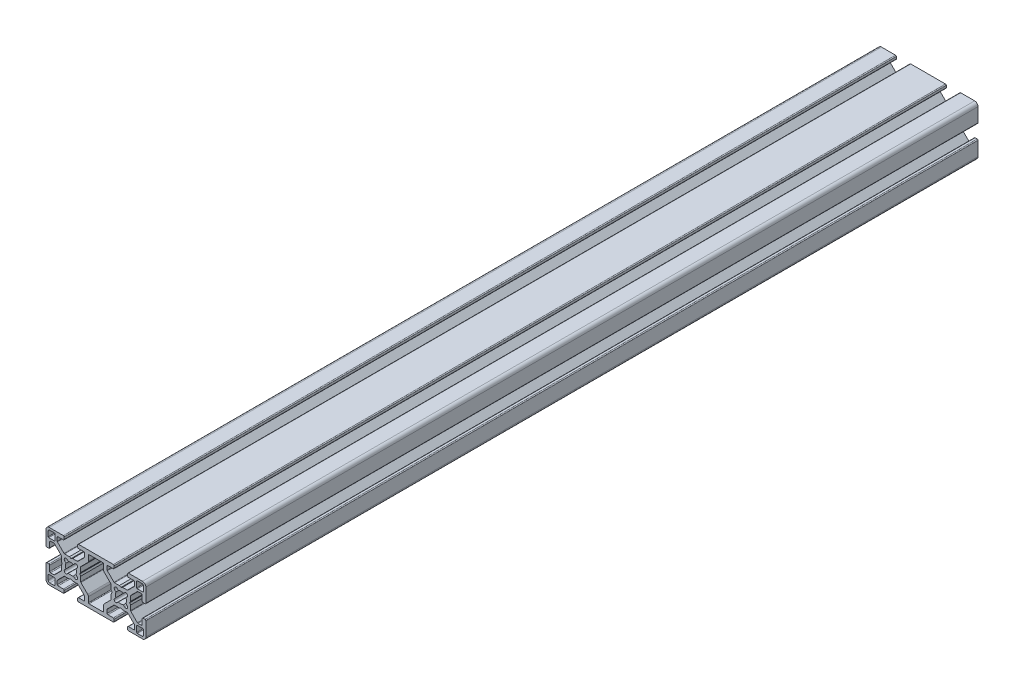
SolidWorks part; units mm, degrees
material "6105-T5 Aluminum"
ref_plane "Front Plane" through (0, 0, 0) normal (0, 0, 1) x (1, 0, 0)
ref_plane "Top Plane" through (0, 0, 0) normal (0, 1, 0) x (1, 0, 0)
ref_plane "Right Plane" through (0, 0, 0) normal (1, 0, 0) x (0, 0, -1)
sketch "Sketch1" plane through (0, 0, 0) normal (0, 0, 1) x (1, 0, 0)
  line L0 (12.7825, 3.7261) -> (13.5257, 2.983)
  line L1 (16.4743, 2.983) -> (17.2175, 3.7261)
  line L2 (18.7261, 2.2175) -> (17.983, 1.4743)
  line L3 (17.983, -1.4743) -> (18.7261, -2.2175)
  line L4 (17.2175, -3.7261) -> (16.4743, -2.983)
  line L5 (13.5257, -2.983) -> (12.7825, -3.7261)
  line L6 (11.2739, -2.2175) -> (12.017, -1.4743)
  line L7 (12.017, 1.4743) -> (11.2739, 2.2175)
  line L8 (-28.7046, 9.8946) -> (-28.7046, 12.6886)
  line L9 (-27.6886, 13.7046) -> (-24.8946, 13.7046)
  line L10 (-24.5136, 13.3236) -> (-24.5136, 9.8946)
  line L11 (-24.8946, 9.5136) -> (-28.3236, 9.5136)
  line L12 (-24.8946, -13.7046) -> (-27.6886, -13.7046)
  line L13 (-28.7046, -12.6886) -> (-28.7046, -9.8946)
  line L14 (-28.3236, -9.5136) -> (-24.8946, -9.5136)
  line L15 (-24.5136, -9.8946) -> (-24.5136, -13.3236)
  line L16 (4.9816, 8.2224) -> (9.0292, 4.1748)
  line L17 (9.178, 3.8155) -> (9.178, 0.9525)
  line L18 (9.178, 0.9525) -> (9.686, 0)
  line L19 (9.686, 0) -> (9.178, -0.9525)
  line L20 (9.178, -0.9525) -> (9.178, -3.8155)
  line L21 (9.0292, -4.1748) -> (4.9816, -8.2224)
  line L22 (4.5352, -9.3) -> (4.5352, -12.4092)
  line L23 (4.1542, -12.7902) -> (-4.1542, -12.7902)
  line L24 (-4.5352, -12.4092) -> (-4.5352, -9.3)
  line L25 (-4.9816, -8.2224) -> (-9.0292, -4.1748)
  line L26 (-9.178, -3.8155) -> (-9.178, -0.9525)
  line L27 (-9.178, -0.9525) -> (-9.686, 0)
  line L28 (-9.686, 0) -> (-9.178, 0.9525)
  line L29 (-9.178, 0.9525) -> (-9.178, 3.8155)
  line L30 (-9.0292, 4.1748) -> (-4.9816, 8.2224)
  line L31 (-4.5352, 9.3) -> (-4.5352, 12.4092)
  line L32 (-4.1542, 12.7902) -> (4.1542, 12.7902)
  line L33 (4.5352, 12.4092) -> (4.5352, 9.3)
  line L34 (-18.7261, -2.2175) -> (-17.983, -1.4743)
  line L35 (-17.983, 1.4743) -> (-18.7261, 2.2175)
  line L36 (-17.2175, 3.7261) -> (-16.4743, 2.983)
  line L37 (-13.5257, 2.983) -> (-12.7825, 3.7261)
  line L38 (-11.2739, 2.2175) -> (-12.017, 1.4743)
  line L39 (-12.017, -1.4743) -> (-11.2739, -2.2175)
  line L40 (-12.7825, -3.7261) -> (-13.5257, -2.983)
  line L41 (-16.4743, -2.983) -> (-17.2175, -3.7261)
  line L42 (24.8946, 13.7046) -> (27.6886, 13.7046)
  line L43 (28.7046, 12.6886) -> (28.7046, 9.8946)
  line L44 (28.3236, 9.5136) -> (24.8946, 9.5136)
  line L45 (24.5136, 9.8946) -> (24.5136, 13.3236)
  line L46 (24.5136, -13.3236) -> (24.5136, -9.8946)
  line L47 (24.8946, -9.5136) -> (28.3236, -9.5136)
  line L48 (28.7046, -9.8946) -> (28.7046, -12.6886)
  line L49 (27.6886, -13.7046) -> (24.8946, -13.7046)
  line L50 (-10.428, -15) -> (10.428, -15)
  line L51 (10.936, -14.492) -> (10.936, -13.2982)
  line L52 (10.428, -12.7902) -> (7.253, -12.7902)
  line L53 (6.745, -12.2822) -> (6.745, -10.2615)
  line L54 (6.8938, -9.9023) -> (10.8252, -5.9708)
  line L55 (11.1845, -5.822) -> (14.0475, -5.822)
  line L56 (14.0475, -5.822) -> (15, -5.314)
  line L57 (15, -5.314) -> (15.9525, -5.822)
  line L58 (15.9525, -5.822) -> (18.8155, -5.822)
  line L59 (19.1748, -5.9708) -> (23.1062, -9.9023)
  line L60 (23.255, -10.2615) -> (23.255, -12.2822)
  line L61 (22.747, -12.7902) -> (19.572, -12.7902)
  line L62 (19.064, -13.2982) -> (19.064, -14.492)
  line L63 (19.572, -15) -> (27.9934, -15)
  line L64 (30, -12.9934) -> (30, -4.572)
  line L65 (29.492, -4.064) -> (28.2982, -4.064)
  line L66 (27.7902, -4.572) -> (27.7902, -7.747)
  line L67 (27.2822, -8.255) -> (25.2615, -8.255)
  line L68 (24.9023, -8.1062) -> (20.9708, -4.1748)
  line L69 (20.822, -3.8155) -> (20.822, -0.9525)
  line L70 (20.822, -0.9525) -> (20.314, 0)
  line L71 (20.314, 0) -> (20.822, 0.9525)
  line L72 (20.822, 0.9525) -> (20.822, 3.8155)
  line L73 (20.9708, 4.1748) -> (24.9023, 8.1062)
  line L74 (25.2615, 8.255) -> (27.2822, 8.255)
  line L75 (27.7902, 7.747) -> (27.7902, 4.572)
  line L76 (28.2982, 4.064) -> (29.492, 4.064)
  line L77 (30, 4.572) -> (30, 12.9934)
  line L78 (27.9934, 15) -> (19.572, 15)
  line L79 (19.064, 14.492) -> (19.064, 13.2982)
  line L80 (19.572, 12.7902) -> (22.747, 12.7902)
  line L81 (23.255, 12.2822) -> (23.255, 10.2615)
  line L82 (23.1062, 9.9023) -> (19.1748, 5.9708)
  line L83 (18.8155, 5.822) -> (15.9525, 5.822)
  line L84 (15.9525, 5.822) -> (15, 5.314)
  line L85 (15, 5.314) -> (14.0475, 5.822)
  line L86 (14.0475, 5.822) -> (11.1845, 5.822)
  line L87 (10.8252, 5.9708) -> (6.8938, 9.9023)
  line L88 (6.745, 10.2615) -> (6.745, 12.2822)
  line L89 (7.253, 12.7902) -> (10.428, 12.7902)
  line L90 (10.936, 13.2982) -> (10.936, 14.492)
  line L91 (10.428, 15) -> (-10.428, 15)
  line L92 (-10.936, 14.492) -> (-10.936, 13.2982)
  line L93 (-10.428, 12.7902) -> (-7.253, 12.7902)
  line L94 (-6.745, 12.2822) -> (-6.745, 10.2615)
  line L95 (-6.8938, 9.9023) -> (-10.8252, 5.9708)
  line L96 (-11.1845, 5.822) -> (-14.0475, 5.822)
  line L97 (-14.0475, 5.822) -> (-15, 5.314)
  line L98 (-15, 5.314) -> (-15.9525, 5.822)
  line L99 (-15.9525, 5.822) -> (-18.8155, 5.822)
  line L100 (-19.1748, 5.9708) -> (-23.1062, 9.9023)
  line L101 (-23.255, 10.2615) -> (-23.255, 12.2822)
  line L102 (-22.747, 12.7902) -> (-19.572, 12.7902)
  line L103 (-19.064, 13.2982) -> (-19.064, 14.492)
  line L104 (-19.572, 15) -> (-27.9934, 15)
  line L105 (-30, 12.9934) -> (-30, 4.572)
  line L106 (-29.492, 4.064) -> (-28.2982, 4.064)
  line L107 (-27.7902, 4.572) -> (-27.7902, 7.747)
  line L108 (-27.2822, 8.255) -> (-25.2615, 8.255)
  line L109 (-24.9023, 8.1062) -> (-20.9708, 4.1748)
  line L110 (-20.822, 3.8155) -> (-20.822, 0.9525)
  line L111 (-20.822, 0.9525) -> (-20.314, 0)
  line L112 (-20.314, 0) -> (-20.822, -0.9525)
  line L113 (-20.822, -0.9525) -> (-20.822, -3.8155)
  line L114 (-20.9708, -4.1748) -> (-24.9023, -8.1062)
  line L115 (-25.2615, -8.255) -> (-27.2822, -8.255)
  line L116 (-27.7902, -7.747) -> (-27.7902, -4.572)
  line L117 (-28.2982, -4.064) -> (-29.492, -4.064)
  line L118 (-30, -4.572) -> (-30, -12.9934)
  line L119 (-27.9934, -15) -> (-19.572, -15)
  line L120 (-19.064, -14.492) -> (-19.064, -13.2982)
  line L121 (-19.572, -12.7902) -> (-22.747, -12.7902)
  line L122 (-23.255, -12.2822) -> (-23.255, -10.2615)
  line L123 (-23.1062, -9.9023) -> (-19.1748, -5.9708)
  line L124 (-18.8155, -5.822) -> (-15.9525, -5.822)
  line L125 (-15.9525, -5.822) -> (-15, -5.314)
  line L126 (-15, -5.314) -> (-14.0475, -5.822)
  line L127 (-14.0475, -5.822) -> (-11.1845, -5.822)
  line L128 (-10.8252, -5.9708) -> (-6.8938, -9.9023)
  line L129 (-6.745, -10.2615) -> (-6.745, -12.2822)
  line L130 (-7.253, -12.7902) -> (-10.428, -12.7902)
  line L131 (-10.936, -13.2982) -> (-10.936, -14.492)
  arc A0 (12.7825, 3.7261) -> (11.2739, 2.2175) centre (12.0282, 2.9718) ccw
  arc A1 (16.4743, 2.983) -> (13.5257, 2.983) centre (15, 0) ccw
  arc A2 (18.7261, 2.2175) -> (17.2175, 3.7261) centre (17.9718, 2.9718) ccw
  arc A3 (17.983, -1.4743) -> (17.983, 1.4743) centre (15, 0) ccw
  arc A4 (17.2175, -3.7261) -> (18.7261, -2.2175) centre (17.9718, -2.9718) ccw
  arc A5 (13.5257, -2.983) -> (16.4743, -2.983) centre (15, 0) ccw
  arc A6 (11.2739, -2.2175) -> (12.7825, -3.7261) centre (12.0282, -2.9718) ccw
  arc A7 (12.017, 1.4743) -> (12.017, -1.4743) centre (15, 0) ccw
  arc A8 (-28.7046, 9.8946) -> (-28.3236, 9.5136) centre (-28.3236, 9.8946) ccw
  arc A9 (-27.6886, 13.7046) -> (-28.7046, 12.6886) centre (-27.6886, 12.6886) ccw
  arc A10 (-24.5136, 13.3236) -> (-24.8946, 13.7046) centre (-24.8946, 13.3236) ccw
  arc A11 (-24.8946, 9.5136) -> (-24.5136, 9.8946) centre (-24.8946, 9.8946) ccw
  arc A12 (-24.8946, -13.7046) -> (-24.5136, -13.3236) centre (-24.8946, -13.3236) ccw
  arc A13 (-28.7046, -12.6886) -> (-27.6886, -13.7046) centre (-27.6886, -12.6886) ccw
  arc A14 (-28.3236, -9.5136) -> (-28.7046, -9.8946) centre (-28.3236, -9.8946) ccw
  arc A15 (-24.5136, -9.8946) -> (-24.8946, -9.5136) centre (-24.8946, -9.8946) ccw
  arc A16 (4.5352, 9.3) -> (4.9816, 8.2224) centre (6.0592, 9.3) ccw
  arc A17 (9.178, 3.8155) -> (9.0292, 4.1748) centre (8.67, 3.8155) ccw
  arc A18 (9.0292, -4.1748) -> (9.178, -3.8155) centre (8.67, -3.8155) ccw
  arc A19 (4.9816, -8.2224) -> (4.5352, -9.3) centre (6.0592, -9.3) ccw
  arc A20 (4.1542, -12.7902) -> (4.5352, -12.4092) centre (4.1542, -12.4092) ccw
  arc A21 (-4.5352, -12.4092) -> (-4.1542, -12.7902) centre (-4.1542, -12.4092) ccw
  arc A22 (-4.5352, -9.3) -> (-4.9816, -8.2224) centre (-6.0592, -9.3) ccw
  arc A23 (-9.178, -3.8155) -> (-9.0292, -4.1748) centre (-8.67, -3.8155) ccw
  arc A24 (-9.0292, 4.1748) -> (-9.178, 3.8155) centre (-8.67, 3.8155) ccw
  arc A25 (-4.9816, 8.2224) -> (-4.5352, 9.3) centre (-6.0592, 9.3) ccw
  arc A26 (-4.1542, 12.7902) -> (-4.5352, 12.4092) centre (-4.1542, 12.4092) ccw
  arc A27 (4.5352, 12.4092) -> (4.1542, 12.7902) centre (4.1542, 12.4092) ccw
  arc A28 (-18.7261, -2.2175) -> (-17.2175, -3.7261) centre (-17.9718, -2.9718) ccw
  arc A29 (-17.983, 1.4743) -> (-17.983, -1.4743) centre (-15, 0) ccw
  arc A30 (-17.2175, 3.7261) -> (-18.7261, 2.2175) centre (-17.9718, 2.9718) ccw
  arc A31 (-13.5257, 2.983) -> (-16.4743, 2.983) centre (-15, 0) ccw
  arc A32 (-11.2739, 2.2175) -> (-12.7825, 3.7261) centre (-12.0282, 2.9718) ccw
  arc A33 (-12.017, -1.4743) -> (-12.017, 1.4743) centre (-15, 0) ccw
  arc A34 (-12.7825, -3.7261) -> (-11.2739, -2.2175) centre (-12.0282, -2.9718) ccw
  arc A35 (-16.4743, -2.983) -> (-13.5257, -2.983) centre (-15, 0) ccw
  arc A36 (24.8946, 13.7046) -> (24.5136, 13.3236) centre (24.8946, 13.3236) ccw
  arc A37 (28.7046, 12.6886) -> (27.6886, 13.7046) centre (27.6886, 12.6886) ccw
  arc A38 (28.3236, 9.5136) -> (28.7046, 9.8946) centre (28.3236, 9.8946) ccw
  arc A39 (24.5136, 9.8946) -> (24.8946, 9.5136) centre (24.8946, 9.8946) ccw
  arc A40 (24.5136, -13.3236) -> (24.8946, -13.7046) centre (24.8946, -13.3236) ccw
  arc A41 (24.8946, -9.5136) -> (24.5136, -9.8946) centre (24.8946, -9.8946) ccw
  arc A42 (28.7046, -9.8946) -> (28.3236, -9.5136) centre (28.3236, -9.8946) ccw
  arc A43 (27.6886, -13.7046) -> (28.7046, -12.6886) centre (27.6886, -12.6886) ccw
  arc A44 (10.428, -15) -> (10.936, -14.492) centre (10.428, -14.492) ccw
  arc A45 (10.936, -13.2982) -> (10.428, -12.7902) centre (10.428, -13.2982) ccw
  arc A46 (6.745, -12.2822) -> (7.253, -12.7902) centre (7.253, -12.2822) ccw
  arc A47 (6.8938, -9.9023) -> (6.745, -10.2615) centre (7.253, -10.2615) ccw
  arc A48 (11.1845, -5.822) -> (10.8252, -5.9708) centre (11.1845, -6.33) ccw
  arc A49 (19.1748, -5.9708) -> (18.8155, -5.822) centre (18.8155, -6.33) ccw
  arc A50 (23.255, -10.2615) -> (23.1062, -9.9023) centre (22.747, -10.2615) ccw
  arc A51 (22.747, -12.7902) -> (23.255, -12.2822) centre (22.747, -12.2822) ccw
  arc A52 (19.572, -12.7902) -> (19.064, -13.2982) centre (19.572, -13.2982) ccw
  arc A53 (19.064, -14.492) -> (19.572, -15) centre (19.572, -14.492) ccw
  arc A54 (27.9934, -15) -> (30, -12.9934) centre (27.9934, -12.9934) ccw
  arc A55 (30, -4.572) -> (29.492, -4.064) centre (29.492, -4.572) ccw
  arc A56 (28.2982, -4.064) -> (27.7902, -4.572) centre (28.2982, -4.572) ccw
  arc A57 (27.2822, -8.255) -> (27.7902, -7.747) centre (27.2822, -7.747) ccw
  arc A58 (24.9023, -8.1062) -> (25.2615, -8.255) centre (25.2615, -7.747) ccw
  arc A59 (20.822, -3.8155) -> (20.9708, -4.1748) centre (21.33, -3.8155) ccw
  arc A60 (20.9708, 4.1748) -> (20.822, 3.8155) centre (21.33, 3.8155) ccw
  arc A61 (25.2615, 8.255) -> (24.9023, 8.1062) centre (25.2615, 7.747) ccw
  arc A62 (27.7902, 7.747) -> (27.2822, 8.255) centre (27.2822, 7.747) ccw
  arc A63 (27.7902, 4.572) -> (28.2982, 4.064) centre (28.2982, 4.572) ccw
  arc A64 (29.492, 4.064) -> (30, 4.572) centre (29.492, 4.572) ccw
  arc A65 (30, 12.9934) -> (27.9934, 15) centre (27.9934, 12.9934) ccw
  arc A66 (19.572, 15) -> (19.064, 14.492) centre (19.572, 14.492) ccw
  arc A67 (19.064, 13.2982) -> (19.572, 12.7902) centre (19.572, 13.2982) ccw
  arc A68 (23.255, 12.2822) -> (22.747, 12.7902) centre (22.747, 12.2822) ccw
  arc A69 (23.1062, 9.9023) -> (23.255, 10.2615) centre (22.747, 10.2615) ccw
  arc A70 (18.8155, 5.822) -> (19.1748, 5.9708) centre (18.8155, 6.33) ccw
  arc A71 (10.8252, 5.9708) -> (11.1845, 5.822) centre (11.1845, 6.33) ccw
  arc A72 (6.745, 10.2615) -> (6.8938, 9.9023) centre (7.253, 10.2615) ccw
  arc A73 (7.253, 12.7902) -> (6.745, 12.2822) centre (7.253, 12.2822) ccw
  arc A74 (10.428, 12.7902) -> (10.936, 13.2982) centre (10.428, 13.2982) ccw
  arc A75 (10.936, 14.492) -> (10.428, 15) centre (10.428, 14.492) ccw
  arc A76 (-10.428, 15) -> (-10.936, 14.492) centre (-10.428, 14.492) ccw
  arc A77 (-10.936, 13.2982) -> (-10.428, 12.7902) centre (-10.428, 13.2982) ccw
  arc A78 (-6.745, 12.2822) -> (-7.253, 12.7902) centre (-7.253, 12.2822) ccw
  arc A79 (-6.8938, 9.9023) -> (-6.745, 10.2615) centre (-7.253, 10.2615) ccw
  arc A80 (-11.1845, 5.822) -> (-10.8252, 5.9708) centre (-11.1845, 6.33) ccw
  arc A81 (-19.1748, 5.9708) -> (-18.8155, 5.822) centre (-18.8155, 6.33) ccw
  arc A82 (-23.255, 10.2615) -> (-23.1062, 9.9023) centre (-22.747, 10.2615) ccw
  arc A83 (-22.747, 12.7902) -> (-23.255, 12.2822) centre (-22.747, 12.2822) ccw
  arc A84 (-19.572, 12.7902) -> (-19.064, 13.2982) centre (-19.572, 13.2982) ccw
  arc A85 (-19.064, 14.492) -> (-19.572, 15) centre (-19.572, 14.492) ccw
  arc A86 (-27.9934, 15) -> (-30, 12.9934) centre (-27.9934, 12.9934) ccw
  arc A87 (-30, 4.572) -> (-29.492, 4.064) centre (-29.492, 4.572) ccw
  arc A88 (-28.2982, 4.064) -> (-27.7902, 4.572) centre (-28.2982, 4.572) ccw
  arc A89 (-27.2822, 8.255) -> (-27.7902, 7.747) centre (-27.2822, 7.747) ccw
  arc A90 (-24.9023, 8.1062) -> (-25.2615, 8.255) centre (-25.2615, 7.747) ccw
  arc A91 (-20.822, 3.8155) -> (-20.9708, 4.1748) centre (-21.33, 3.8155) ccw
  arc A92 (-20.9708, -4.1748) -> (-20.822, -3.8155) centre (-21.33, -3.8155) ccw
  arc A93 (-25.2615, -8.255) -> (-24.9023, -8.1062) centre (-25.2615, -7.747) ccw
  arc A94 (-27.7902, -7.747) -> (-27.2822, -8.255) centre (-27.2822, -7.747) ccw
  arc A95 (-27.7902, -4.572) -> (-28.2982, -4.064) centre (-28.2982, -4.572) ccw
  arc A96 (-29.492, -4.064) -> (-30, -4.572) centre (-29.492, -4.572) ccw
  arc A97 (-30, -12.9934) -> (-27.9934, -15) centre (-27.9934, -12.9934) ccw
  arc A98 (-19.572, -15) -> (-19.064, -14.492) centre (-19.572, -14.492) ccw
  arc A99 (-19.064, -13.2982) -> (-19.572, -12.7902) centre (-19.572, -13.2982) ccw
  arc A100 (-23.255, -12.2822) -> (-22.747, -12.7902) centre (-22.747, -12.2822) ccw
  arc A101 (-23.1062, -9.9023) -> (-23.255, -10.2615) centre (-22.747, -10.2615) ccw
  arc A102 (-18.8155, -5.822) -> (-19.1748, -5.9708) centre (-18.8155, -6.33) ccw
  arc A103 (-10.8252, -5.9708) -> (-11.1845, -5.822) centre (-11.1845, -6.33) ccw
  arc A104 (-6.745, -10.2615) -> (-6.8938, -9.9023) centre (-7.253, -10.2615) ccw
  arc A105 (-7.253, -12.7902) -> (-6.745, -12.2822) centre (-7.253, -12.2822) ccw
  arc A106 (-10.428, -12.7902) -> (-10.936, -13.2982) centre (-10.428, -13.2982) ccw
  arc A107 (-10.936, -14.492) -> (-10.428, -15) centre (-10.428, -14.492) ccw
extrude "Extrude1" add sketch "Sketch1" against normal blind 500
